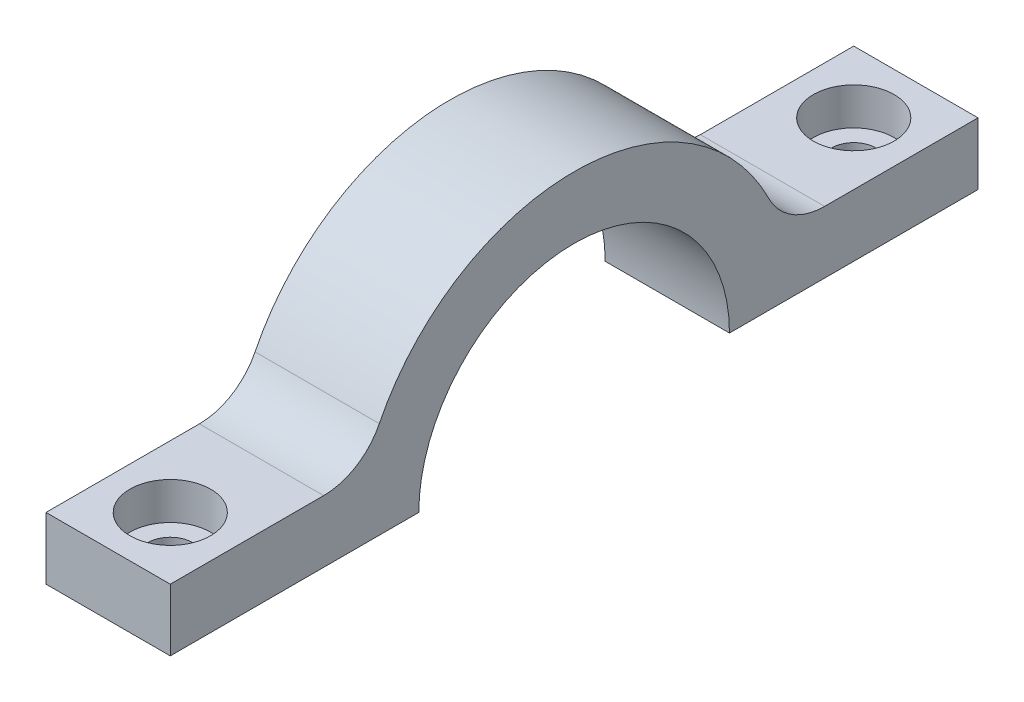
SolidWorks part; units mm, degrees
ref_plane "Front Plane" through (0, 0, 0) normal (0, 0, 1) x (1, 0, 0)
ref_plane "Top Plane" through (0, 0, 0) normal (0, 1, 0) x (1, 0, 0)
ref_plane "Right Plane" through (0, 0, 0) normal (1, 0, 0) x (0, 0, -1)
sketch "Sketch1" plane through (0, 0, 0) normal (1, 0, 0) x (0, 0, -1)
  line L2 (-32.5, 0) -> (-12.5, 0)
  line L5 (32.5, 0) -> (12.5, 0)
  line L6 (-32.5, 5) -> (-16.7705, 5)
  line L7 (32.5, 5) -> (16.7705, 5)
  line L8 (-32.5, 5) -> (-32.5, 0)
  line L9 (32.5, 5) -> (32.5, 0)
  arc A0 (-12.5, 0) -> (12.5, 0) centre (0, 0) cw
  arc A2 (-16.7705, 5) -> (16.7705, 5) centre (0, 0) cw
  dimension "D1" = 5
  dimension "D2" = 65
  dimension "D3" = 25
extrude "Boss-Extrude1" add sketch "Sketch1" along normal mid plane 10
hole_wizard "CBORE for M3 SHCS1" positions "Sketch2" profile "Sketch3" counterbore size "M3" standard "ANSI Metric"
sketch "Sketch2" plane through (-41.05, 5, 0) normal (0, 1, 0) x (1, 0, 0)
  point P0 (41.05, -27.5)
  point P2 (41.05, 27.5)
  point P4 (0, 0)
sketch "Sketch3" plane through (0, 5, 27.5) normal (1, 0, 0) x (0, 0, 1)
  line L0 (0, 0) -> (0, 6.0815)
  line L1 (0, 6.0815) -> (1.8, 5)
  line L2 (1.8, 5) -> (1.8, 3)
  line L3 (1.8, 3) -> (3.25, 3)
  line L4 (3.25, 3) -> (3.25, 0)
  line L5 (3.25, 0) -> (0, 0)
  line L6 (0, 6.0815) -> (-1.8, 5) construction
  line L7 (0, -6.35) -> (0, 107.95) construction
  dimension "Hole Dia." = 3.6
  dimension "Hole Depth" = 5
  dimension "C'Bore Dia." = 6.5
  dimension "C'Bore Depth" = 3
  dimension "Drill Angle" = 118
fillet "Fillet1" radius 5 2 edges at (0, 5, -16.7705) (0, 5, 16.7705)
